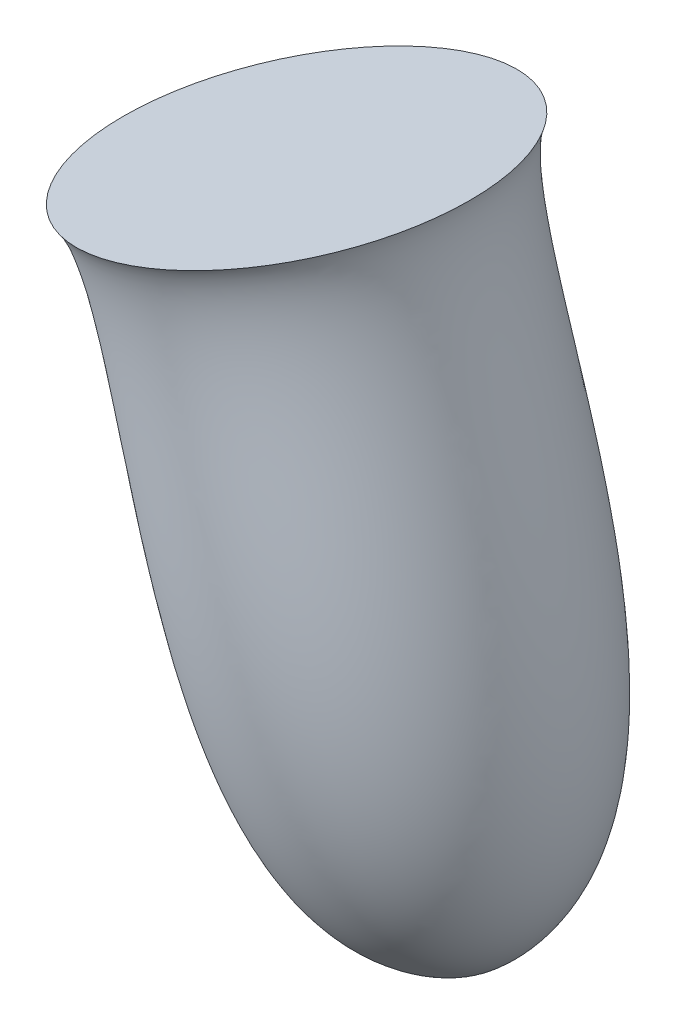
SolidWorks part; units mm, degrees
ref_plane "Alzado" through (0, 0, 0) normal (0, 0, 1) x (1, 0, 0)
ref_plane "Planta" through (0, 0, 0) normal (0, 1, 0) x (1, 0, 0)
ref_plane "Vista lateral" through (0, 0, 0) normal (1, 0, 0) x (0, 0, -1)
sketch "Croquis1" plane through (0, 0, 0) normal (0, 0, 1) x (1, 0, 0)
  line L0 (-105.1062, 41.2676) -> (-80.9495, -42.0225) construction
  line L1 (-128.6142, 34.4496) -> (-79.2097, 48.7784) construction
  line L2 (-128.6142, 34.4496) -> (-105.1062, 41.2676)
  line L3 (-105.1062, 41.2676) -> (-80.9495, -42.0225)
  line L4 (-128.6142, 34.4496) -> (-128.6142, 104.4496) construction
  line L5 (-128.6142, 104.4496) -> (-103.2045, 104.4496) construction
  spline S0 degree 3 poles (-128.6142, 34.4496) (-118.0246, 25.5033) (-115.6197, -44.557) (-80.9495, -42.0225) knots 0 0 0 0 1 1 1 1
  dimension "D2" = 70
  dimension "D1" = 86.7224
revolve "Revolución1" add sketch "Croquis1" angle 360 about L3
sketch "Croquis2" plane through (-19.1954, 66.1843, 0) normal (-0.2786, 0.9604, 0) x (0.9604, 0.2786, 0)
  line L0 (-113.9279, 0) -> (-65.0233, -1.5488)
  circle A0 centre (-89.4511, 0) radius 24.4768 construction
ref_plane "Plano1" through (-0.1096, -0.0318, 3.6044) normal (-0.0304, -0.0088, 0.9995) x (0.9599, 0.2784, 0.0317)
